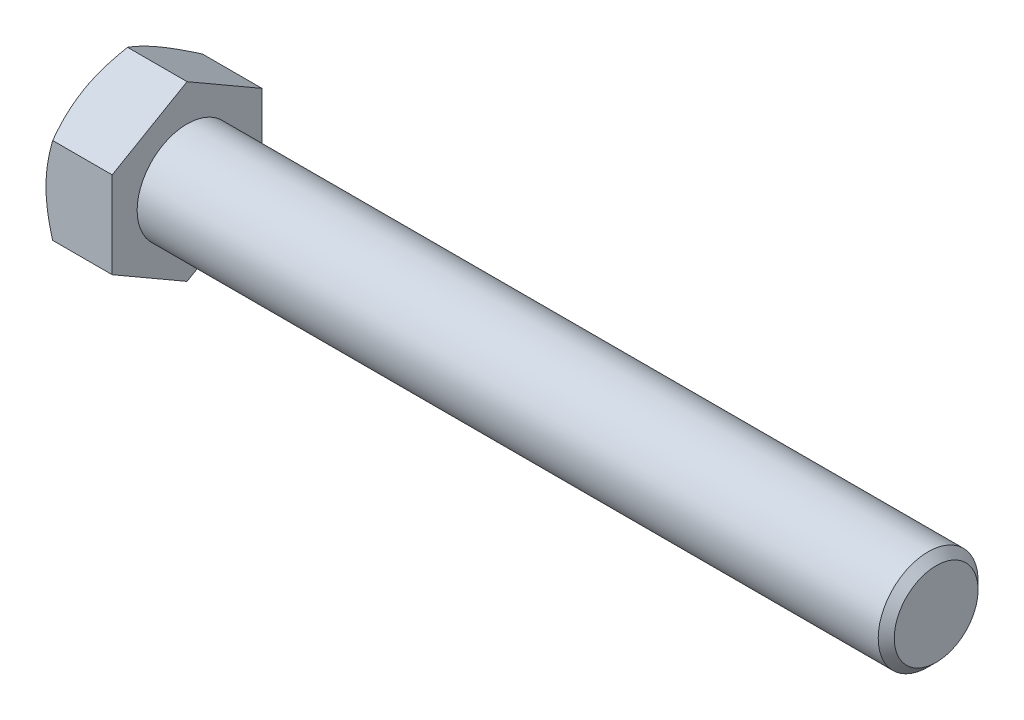
SolidWorks part; units mm, degrees
extrude "BaseHead" add sketch "Sketch1" along normal blind 7.95
sketch "Sketch1" plane through (0, 0, 0) normal (1, 0, 0) x (0, 0, -1)
  line L0 (9, 5.1962) -> (9, -5.1962)
  line L1 (-9, 5.1962) -> (-9, -5.1962)
  line L2 (9, -5.1962) -> (0, -10.3923)
  line L3 (0, -10.3923) -> (-9, -5.1962)
  line L4 (9, 5.1962) -> (0, 10.3923)
  line L5 (0, 10.3923) -> (-9, 5.1962)
  dimension "Width_flats" = 18
  dimension "D2" = 120
  dimension "D3" = 9
  dimension "D4" = 9
  dimension "D5" = 9
ref_plane "Plane1" through (0, 0, 0) normal (0, 0, 1) x (1, 0, 0)
ref_plane "Plane2" through (0, 0, 0) normal (0, 1, 0) x (1, 0, 0)
ref_plane "Plane3" through (0, 0, 0) normal (1, 0, 0) x (0, 0, -1)
sketch "BodySke" plane through (0, 0, 0) normal (0, 0, 1) x (1, 0, 0)
  line L0 (0, 5.1962) -> (0, -5.1962) construction
  line L1 (0, 0) -> (97.95, 0)
  line L2 (0, 0) -> (0, 6)
  line L3 (0, 6) -> (96.986, 6)
  line L4 (97.95, 0) -> (97.95, 5.036)
  line L5 (7.95, 10.3923) -> (7.95, 5.1962) construction
  line L6 (97.95, 5.036) -> (96.986, 6)
  line L7 (0, 0) -> (96.52, 0) construction
  line L8 (97.95, -5.036) -> (96.986, -6) construction
  line L9 (0, -6) -> (96.986, -6) construction
  line L10 (9.7, 15.24) -> (9.7, -1.27) construction
  line L11 (67.95, 15.24) -> (67.95, -1.27) construction
  line L12 (7.95, 5.1962) -> (7.95, -5.1962) construction
  dimension "Diameter" = 12
revolve "BaseBody" add sketch "BodySke"
cosmetic thread "ThreadCosmetic" [suppressed]
fillet "HeadFillet" [suppressed] radius 0.6
sketch "Sketch3" plane through (0, 0, 0) normal (0, 0, 1) x (1, 0, 0)
  line L0 (0, 9) -> (3.6906, 15.3923)
  line L1 (0, 10.3923) -> (0, 5.1962) construction
  line L2 (3.6906, 15.3923) -> (3.6906, 20.3923)
  line L3 (3.6906, 20.3923) -> (-10, 20.3923)
  line L4 (-10, 20.3923) -> (-10, 9)
  line L5 (-10, 9) -> (0, 9)
  line L6 (0, 0) -> (99.06, 0) construction
  line L7 (7.95, 10.3923) -> (0, 10.3923) construction
  dimension "D1" = 9
  dimension "D2" = 5
  dimension "D3" = 10
  dimension "D4" = 5
  dimension "Head_ch_ang" = 30
revolve "HeadChamfer" cut sketch "Sketch3" angle 360 about L6
sketch "ThdSchSke" plane through (0, 0, 0) normal (0, 0, 1) x (1, 0, 0)
  line L0 (67.95, -5.036) -> (67.275, -6)
  line L1 (67.95, -5.036) -> (68.625, -6)
  line L2 (68.625, -6) -> (68.625, -7.5)
  line L3 (-3.175, 0) -> (5.1513, 0) construction
  line L5 (68.625, -7.5) -> (67.275, -7.5)
  line L6 (67.275, -7.5) -> (67.275, -6)
  dimension "Thread_minor" = 10.072
  dimension "Diameter" = 12
  dimension "Start" = 67.95
revolve "ThreadSchematic" [suppressed] cut sketch "ThdSchSke" angle 360 about L3
pattern_linear "ThdSchPat" [suppressed]
equation "\"D3@Sketch1\" = \"Width_flats@Sketch1\" / 2"
equation "\"D4@Sketch1\" = \"D3@Sketch1\""
equation "\"D5@Sketch1\" = \"D4@Sketch1\""
equation "\"Thread_minor@ThreadCosmetic\" = \"Minor_dia@BodySke\""
equation "\"D1@Sketch3\" = \"Width_flats@Sketch1\" / 2"
equation "' \"D1@Sketch4\" = \"Width_flats@Sketch1\""
equation "\"Thread_length@ThreadCosmetic\" = ((sgn( (\"Length@BodySke\" - \"Advance@BodySke\" ) - \"Thread_nom@BodySke\" )-1)*( (\"Length@BodySke\" - \"Advance@BodySke\" ) - \"Thread_nom@BodySke\" ))/-2+ \"Thread_nom@BodySke\""
equation "\"Thread_minor@ThdSchSke\" = \"Minor_dia@BodySke\""
equation "\"Diameter@ThdSchSke\" = \"Diameter@BodySke\""
equation "\"Overcut@ThdSchSke\" = \"Diameter@BodySke\" * 1.25"
equation "\"Start@ThdSchSke\" = \"Head_ht@BaseHead\" + \"Length@BodySke\" - \"Thread_length@ThreadCosmetic\"  '---Non-countersunk---"
equation "\"Num_threads@ThdSchPat\" = int( \"Thread_length@ThreadCosmetic\" / \"Advance@BodySke\" + 0.999 )  + 1"
equation "\"Advance@ThdSchPat\" = \"Thread_length@ThreadCosmetic\" /  (\"Num_threads@ThdSchPat\" - 1) 'relax it"
equation "\"Num_threads@ThdSchPat\" = \"Num_threads@ThdSchPat\" - sgn( \"Num_threads@ThdSchPat\" - 1) '---chamfered tips only---"
